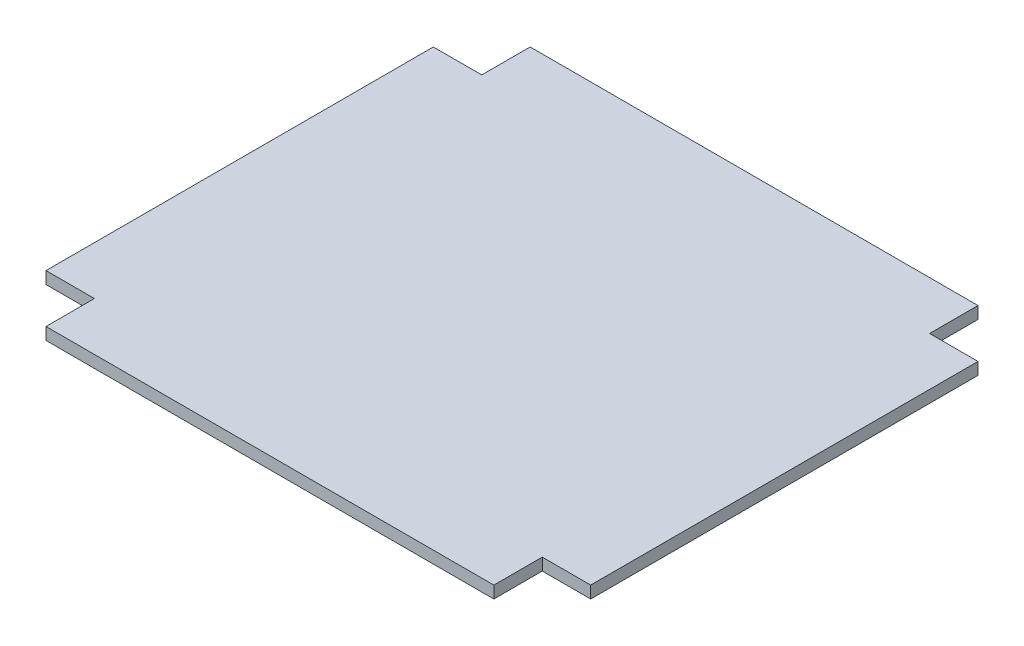
SolidWorks part; units mm, degrees
ref_plane "Alzado" through (0, 0, 0) normal (0, 0, 1) x (1, 0, 0)
ref_plane "Planta" through (0, 0, 0) normal (0, 1, 0) x (1, 0, 0)
ref_plane "Vista lateral" through (0, 0, 0) normal (1, 0, 0) x (0, 0, -1)
sketch "Croquis1" plane through (0, 0, 0) normal (0, 1, 0) x (1, 0, 0)
  line L0 (3.175, -127) -> (3.175, 127) construction
  line L5 (-139.7, 127) -> (146.05, 127)
  line L6 (-139.7, 127) -> (-139.7, -127)
  line L7 (-139.7, -127) -> (146.05, -127)
  line L8 (146.05, 127) -> (146.05, -127)
  line L9 (-139.7, -127) -> (-114.3, -127)
  line L10 (-139.7, -127) -> (-139.7, -101.6)
  line L11 (-139.7, 127) -> (-114.3, 127)
  line L12 (-139.7, 127) -> (-139.7, 101.6)
  line L13 (-139.7, 101.6) -> (-114.3, 101.6)
  line L14 (-114.3, 127) -> (-114.3, 101.6)
  line L15 (-139.7, -101.6) -> (-114.3, -101.6)
  line L16 (-114.3, -127) -> (-114.3, -101.6)
  line L17 (146.05, -127) -> (120.65, -127)
  line L18 (146.05, -127) -> (146.05, -101.6)
  line L19 (146.05, -101.6) -> (120.65, -101.6)
  line L20 (120.65, -127) -> (120.65, -101.6)
  line L21 (146.05, 127) -> (120.65, 127)
  line L22 (146.05, 127) -> (146.05, 101.6)
  line L23 (146.05, 101.6) -> (120.65, 101.6)
  line L24 (120.65, 127) -> (120.65, 101.6)
  line L25 (-139.7, 0) -> (146.05, 0) construction
  point P0 (0, 0)
  dimension "D1" = 254
  dimension "D2" = 285.75
  dimension "D3" = 25.4
  dimension "D4" = 25.4
  dimension "D5" = 25.4
  dimension "D6" = 25.4
  dimension "D7" = 25.4
  dimension "D8" = 25.4
  dimension "D9" = 25.4
  dimension "D10" = 25.4
extrude "Saliente-Extruir1" add sketch "Croquis1" along normal blind 6.35 contours L24 L5 L14 L13 L6 L15 L16 L7 L20 L19 L8 L23
